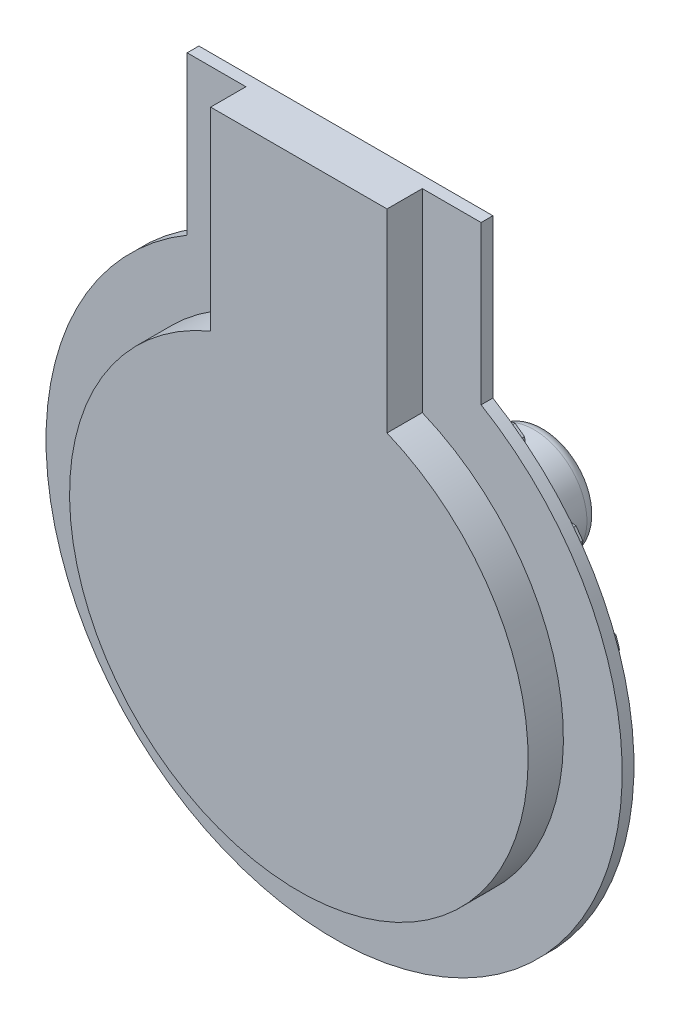
SolidWorks part; units mm, degrees
ref_plane "Ön Düzlem" through (0, 0, 0) normal (0, 0, 1) x (1, 0, 0)
ref_plane "Üst Düzlem" through (0, 0, 0) normal (0, 1, 0) x (1, 0, 0)
ref_plane "Sağ Düzlem" through (0, 0, 0) normal (1, 0, 0) x (0, 0, -1)
sketch "Çizim1" plane through (0, 0, 0) normal (0, 0, 1) x (1, 0, 0)
  line L0 (-2560, 390) -> (-2560, 225) construction
  line L1 (-2710, 225) -> (-2710, 390) construction
  line L2 (-2560, 390) -> (-2560, 225)
  line L3 (-2710, 225) -> (-2710, 390)
  line L4 (-2560, 390) -> (-2710, 390)
  arc A0 (-2710, 225) -> (-2560, 225) centre (-2635, 45) ccw construction
  arc A1 (-2710, 225) -> (-2560, 225) centre (-2635, 45) ccw
extrude "Yükseklik-Ekstrüzyon1" add sketch "Çizim1" against normal up to surface (30 mm away)
ref_plane "Düzlem1" through (-2510, 255.7131, -30) normal (0, -1, 0) x (-1, 0, 0)
sketch "Çizim4" plane through (0, 0, -30) normal (0, 0, -1) x (-1, 0, 0)
  line L0 (2510, 390) -> (2510, 255.7131) construction
  line L1 (2760, 255.7131) -> (2760, 390) construction
  line L2 (2510, 390) -> (2510, 255.7131)
  line L3 (2710, 390) -> (2560, 390)
  line L4 (2560, 390) -> (2560, 225)
  line L5 (2710, 225) -> (2710, 390)
  line L6 (2710, 390) -> (2560, 390)
  line L7 (2560, 390) -> (2560, 225)
  line L8 (2710, 225) -> (2710, 390)
  line L9 (2760, 255.7131) -> (2760, 390)
  line L10 (2510, 390) -> (2760, 390)
  arc A0 (2510, 255.7131) -> (2760, 255.7131) centre (2635, 45) ccw
  arc A1 (2560, 225) -> (2710, 225) centre (2635, 45) ccw
  arc A2 (2560, 225) -> (2710, 225) centre (2635, 45) ccw
  dimension "D1" = 0
extrude "Yükseklik-Ekstrüzyon2" add sketch "Çizim4" along normal up to surface (10 mm away) contours L10 L9 A0 L2
sketch "Çizim5" plane through (0, 0, -40) normal (0, 0, -1) x (-1, 0, 0)
  circle A0 centre (2635, 45) radius 190
  dimension "D1" = 380
extrude "Yükseklik-Ekstrüzyon3" add sketch "Çizim5" along normal blind 20
sketch "Çizim6" plane through (0, 0, -40) normal (0, 0, -1) x (-1, 0, 0)
  line L0 (2635, 290) -> (2635, 235) construction
  line L1 (2639.9706, 250.5) -> (2647, 257.5294)
  line L2 (2647, 267.4706) -> (2639.9706, 274.5)
  line L3 (2639.9706, 274.5) -> (2630.0294, 274.5)
  line L4 (2630.0294, 274.5) -> (2623, 267.4706)
  line L5 (2623, 267.4706) -> (2623, 257.5294)
  line L6 (2623, 257.5294) -> (2630.0294, 250.5)
  line L7 (2630.0294, 250.5) -> (2639.9706, 250.5)
  line L8 (2647, 257.5294) -> (2647, 267.4706)
  circle A0 centre (2635, 45) radius 245 construction
  circle A1 centre (2635, 45) radius 190 construction
  circle A2 centre (2635, 262.5) radius 12 construction
  dimension "D1" = 24
extrude "Yükseklik-Ekstrüzyon4" add sketch "Çizim6" along normal blind 13
pattern_circular "Dairesel Kaplama1" count 20 over 360 about axis through (-2635, 45, 0) along (0, 0, 1) of "Yükseklik-Ekstrüzyon4"
sketch "Çizim7" plane through (0, 0, -60) normal (0, 0, -1) x (-1, 0, 0)
  circle A0 centre (2635, 45) radius 45
  dimension "D1" = 90
extrude "Yükseklik-Ekstrüzyon5" add sketch "Çizim7" along normal blind 150
fillet "Radyus1" radius 10 2 edges at (-2680, 45, -60) (-2680, 45, -210)
